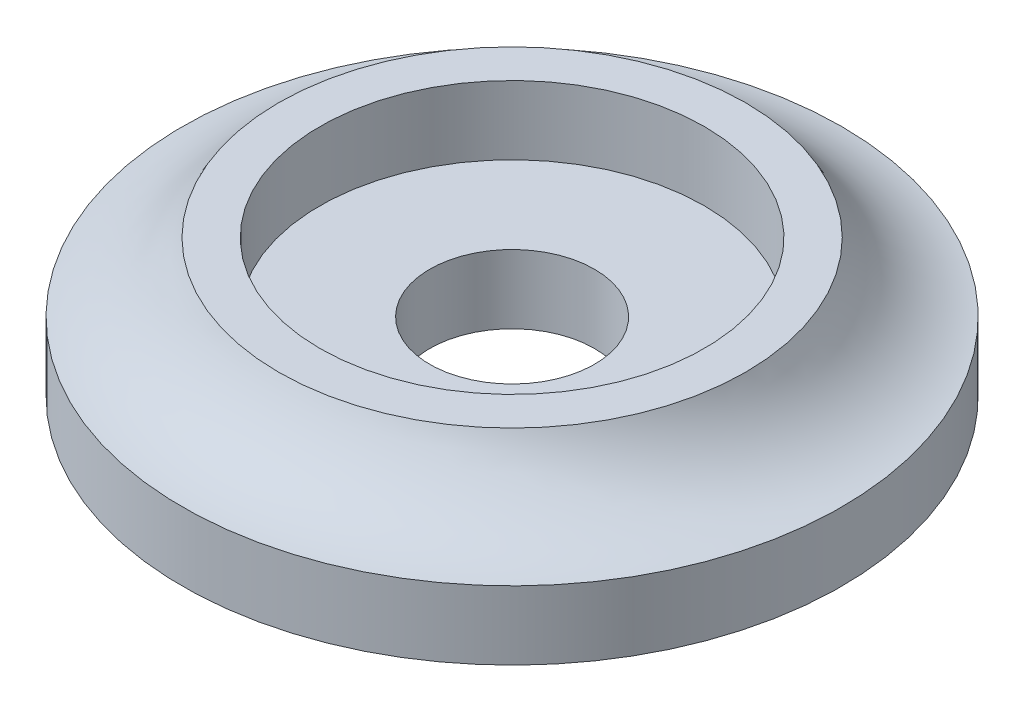
SolidWorks part; units mm, degrees
ref_plane "Front Plane" through (0, 0, 0) normal (0, 0, 1) x (1, 0, 0)
ref_plane "Top Plane" through (0, 0, 0) normal (0, 1, 0) x (1, 0, 0)
ref_plane "Right Plane" through (0, 0, 0) normal (1, 0, 0) x (0, 0, -1)
sketch "Sketch2" plane through (0, 0, 0) normal (1, 0, 0) x (0, 0, -1)
  line L0 (0, 0) -> (0, 15.5284) construction
  line L1 (12, 0) -> (12, 2.5)
  line L2 (3, 0) -> (12, 0)
  line L4 (7, 5) -> (8.5, 5)
  line L5 (12, 0) -> (12, 2.5)
  line L9 (3, 2.5) -> (7, 2.5)
  line L10 (7, 5) -> (7, 2.5)
  line L15 (3, 2.5) -> (3, 0)
  arc A0 (12, 2.5) -> (8.5, 5) centre (12.5557, 6.9779) cw
  point P4 (0, 0)
  dimension "D1" = 7
  dimension "D2" = 1.5
  dimension "D3" = 2.5
  dimension "D4" = 7
revolve "Revolve1" add sketch "Sketch2" angle 360 about L0
